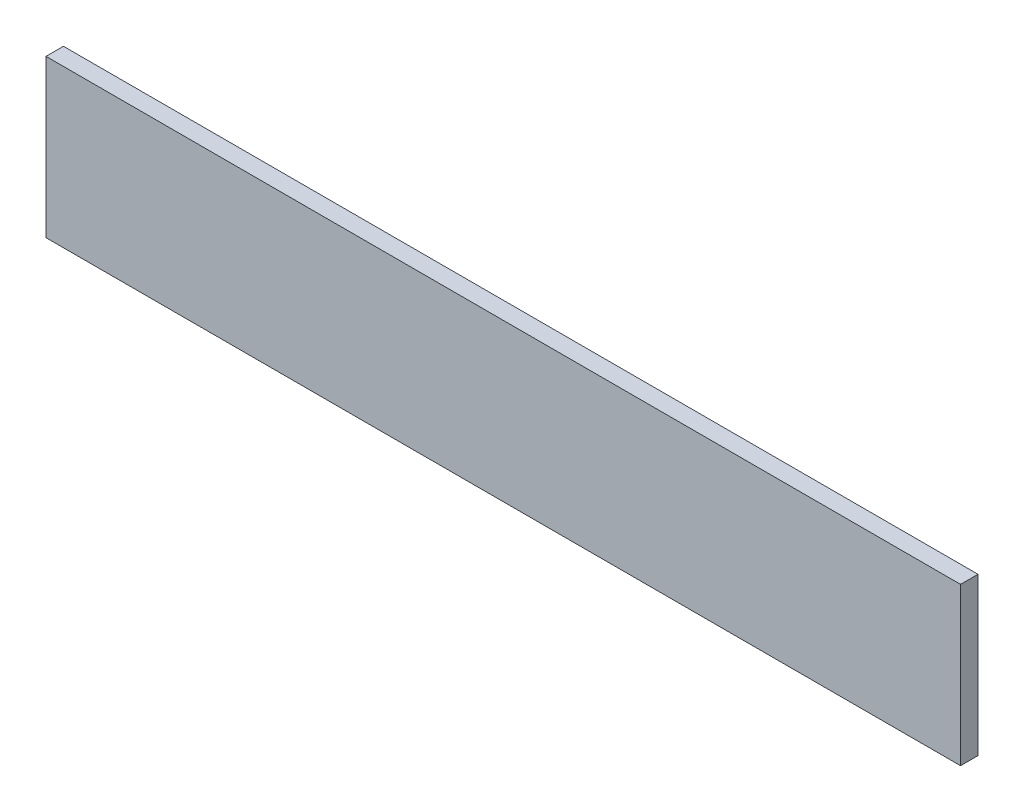
SolidWorks part; units mm, degrees
ref_plane "Plan de face" through (0, 0, 0) normal (0, 0, 1) x (1, 0, 0)
ref_plane "Plan de dessus" through (0, 0, 0) normal (0, 1, 0) x (1, 0, 0)
ref_plane "Plan de droite" through (0, 0, 0) normal (1, 0, 0) x (0, 0, -1)
sketch "Esquisse1" plane through (0, 0, 0) normal (0, 0, 1) x (1, 0, 0)
  line L1 (0, 0) -> (262, 0)
  line L2 (0, 0) -> (0, 45)
  line L3 (0, 45) -> (262, 45)
  line L4 (262, 0) -> (262, 45)
  dimension "D1" = 262
  dimension "D2" = 45
extrude "Boss.-Extru.1" add sketch "Esquisse1" along normal blind 5 contours L2 L1 L4 L3
